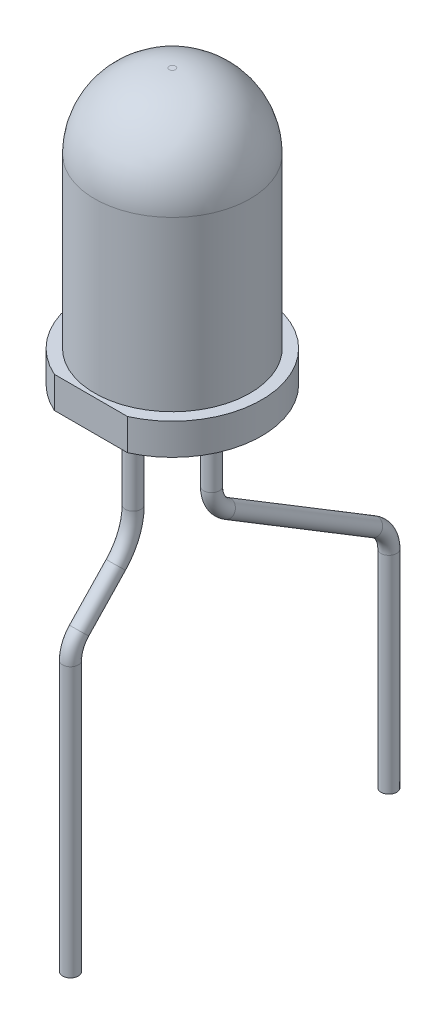
SolidWorks part; units mm, degrees
material "Perspex (TM) GS Acrylic Cast Sheet"
ref_plane "Front Plane" through (0, 0, 0) normal (0, 0, 1) x (1, 0, 0)
ref_plane "Top Plane" through (0, 0, 0) normal (0, 1, 0) x (1, 0, 0)
ref_plane "Right Plane" through (0, 0, 0) normal (1, 0, 0) x (0, 0, -1)
sketch "Sketch1" plane through (0, 0, 0) normal (0, 0, 1) x (1, 0, 0)
  line L0 (0, 0) -> (0, 8.75)
  line L1 (0, 0) -> (2.85, 0)
  line L2 (2.85, 0) -> (2.85, 1)
  line L3 (2.85, 1) -> (2.48, 1)
  line L4 (2.48, 1) -> (2.48, 6.37)
  line L5 (0, 8.75) -> (0.1, 8.75)
  arc A0 (2.48, 6.37) -> (0.1, 8.75) centre (0.1, 6.37) ccw
  dimension "D5" = 0.1
  dimension "D1" = 8.75
  dimension "D2" = 2.85
  dimension "D3" = 2.48
  dimension "D4" = 1
revolve "Revolve1" add sketch "Sketch1" angle 360 about L0
sketch "Sketch2" plane through (0, 0, 0) normal (0, -1, 0) x (1, 0, 0)
  line L0 (0, 0) -> (0, 2.6) construction
  line L1 (-1.1673, 2.6) -> (1.1673, 2.6)
  line L2 (0, 2.6) -> (0, 2.85) construction
  line L3 (0, 0) -> (0, -2.85) construction
  circle A0 centre (0, 0) radius 2.85 construction
  arc A1 (1.1673, 2.6) -> (-1.1673, 2.6) centre (0, 0) ccw
  dimension "D1" = 5.45
extrude "Cut-Extrude1" cut sketch "Sketch2" against normal up to surface (1 mm away) up to face at (0, 1, -2.48)
sketch "Sketch3" plane through (0, 0, 0) normal (0, -1, 0) x (1, 0, 0)
  line L0 (0, 1.25) -> (0, -1.25) construction
  circle A0 centre (0, -1.25) radius 0.25
  circle A1 centre (0, 1.25) radius 0.25
  dimension "D2" = 0.5
  dimension "D1" = 2.5
extrude "Boss-Extrude1" add sketch "Sketch3" along normal blind 2
sketch "Sketch4" plane through (0, 0, 0) normal (1, 0, 0) x (0, 0, -1)
  line L0 (-1.25, -2) -> (-1.25, 0) construction
  line L1 (-1.5, -2) -> (-1, -2) construction
  line L2 (-1.5, 0) -> (-1, 0) construction
  line L3 (1.25, -2) -> (1.25, 0) construction
  line L4 (1, -2) -> (1.5, -2) construction
  line L5 (1, 0) -> (1.5, 0) construction
  line L6 (-1.25, -2) -> (-1.25, -2.7)
  line L7 (-1.8017, -4.0793) -> (-2.9741, -5.3103)
  line L8 (-3.25, -6) -> (-3.25, -14.6)
  line L9 (1.25, -2) -> (1.25, -3.4373) construction
  line L10 (1.7309, -4.2921) -> (6.4291, -7.1453) construction
  line L11 (6.91, -8) -> (6.91, -14.6) construction
  line L12 (-3.25, -14.6) -> (6.91, -14.6) construction
  arc A0 (-1.25, -2.7) -> (-1.8017, -4.0793) centre (-3.25, -2.7) cw
  arc A1 (-2.9741, -5.3103) -> (-3.25, -6) centre (-2.25, -6) ccw
  arc A2 (1.25, -3.4373) -> (1.7309, -4.2921) centre (2.25, -3.4373) ccw construction
  arc A3 (6.4291, -7.1453) -> (6.91, -8) centre (5.91, -8) cw construction
  point P22 (-1.25, -3.5)
  point P25 (-3.25, -5.6)
  point P28 (1.25, -4)
  point P31 (6.91, -7.4373)
  dimension "D8" = 2
  dimension "D9" = 1
  dimension "D10" = 1
  dimension "D11" = 1
  dimension "D1" = 1.5
  dimension "D2" = 2
  dimension "D3" = 9
  dimension "D5" = 2
  dimension "D6" = 10.16
  dimension "D7" = 6
  dimension "D12" = 8
ref_plane "Plane1" through (0, -14.6, 3.25) normal (0, -1, 0) x (-1, 0, 0)
sketch "Sketch5" plane through (0, -14.6, 3.25) normal (0, -1, 0) x (-1, 0, 0)
  circle A0 centre (0, 0) radius 0.25
  dimension "D1" = 0.5
sweep "Sweep1" add profiles "Sketch5" path "Sketch4"
sketch "Sketch6" plane through (0, 0, 0) normal (1, 0, 0) x (0, 0, -1)
  line L0 (6.91, -8) -> (6.91, -14.6) construction
  line L1 (1.7309, -4.2921) -> (6.4291, -7.1453) construction
  line L2 (1.25, -2) -> (1.25, -3.4373) construction
  line L3 (6.91, -8) -> (6.91, -14.6)
  line L4 (1.7309, -4.2921) -> (6.4291, -7.1453)
  line L5 (1.25, -2) -> (1.25, -3.4373)
  arc A0 (6.91, -8) -> (6.4291, -7.1453) centre (5.91, -8) ccw construction
  arc A1 (1.25, -3.4373) -> (1.7309, -4.2921) centre (2.25, -3.4373) ccw construction
  arc A2 (6.91, -8) -> (6.4291, -7.1453) centre (5.91, -8) ccw
  arc A3 (1.25, -3.4373) -> (1.7309, -4.2921) centre (2.25, -3.4373) ccw
ref_plane "Plane2" through (0, -14.6, -6.91) normal (0, -1, 0) x (-1, 0, 0)
sketch "Sketch7" plane through (0, -14.6, -6.91) normal (0, -1, 0) x (-1, 0, 0)
  circle A0 centre (0, 0) radius 0.25
  dimension "D1" = 0.5
sweep "Sweep2" add profiles "Sketch7" path "Sketch6"
sketch "Sketch8" plane through (0, 0, 0) normal (0, -1, 0) x (1, 0, 0)
  circle A0 centre (0, 1.25) radius 0.25 construction
  circle A1 centre (0, 1.25) radius 0.25
  circle A2 centre (0, -1.25) radius 0.25 construction
  circle A3 centre (0, -1.25) radius 0.25
extrude "Boss-Extrude2" add sketch "Sketch8" against normal blind 3 separate body
sketch "Sketch11" plane through (0, 3, 0) normal (0, 1, 0) x (1, 0, 0)
  circle A1 centre (0, 1.25) radius 0.25
  circle A2 centre (0, 1.25) radius 0.25
  dimension "D1" = 0
extrude "Cut-Extrude2" cut sketch "Sketch11" against normal blind 1.5
sketch "Sketch9" plane through (0, 3, 0) normal (0, 1, 0) x (1, 0, 0)
  circle A0 centre (0, -1.25) radius 0.5
  dimension "D1" = 1
extrude "Boss-Extrude3" add sketch "Sketch9" along normal blind 0.2
fillet "Fillet1" radius 0.15 1 edges at (0, 3.2, 1.75)
sketch "Sketch10" plane through (0, 0, 0) normal (1, 0, 0) x (0, 0, -1)
  line L0 (-1.25, 3) -> (-1.25, 1.4)
  line L1 (-1.5, 3) -> (-1, 3) construction
  line L2 (-1.25, 1.4) -> (-0.75, 1.4)
  line L3 (0.3972, 1.7617) -> (1.4079, 2.4694)
  line L4 (1.3898, 2.6433) -> (0.9317, 2.8391)
  line L5 (0.1457, 3) -> (-1.25, 3)
  line L6 (1.45, 2.5617) -> (-1.25, 2.5617) construction
  line L7 (1.5, 1.5) -> (1.5, 2.1)
  line L8 (1.5, 1.5) -> (1.5, 1.1)
  line L9 (1.5, 0) -> (1.5, 1.5) construction
  line L10 (1.5, 1.1) -> (0.9, 1.1)
  line L11 (0.9, 1.1) -> (0.9, 1.7)
  line L12 (0.9, 1.7) -> (1.5, 2.1) construction
  line L13 (1.5, 1.5) -> (1, 1.5) construction
  arc A0 (1.4079, 2.4694) -> (1.3898, 2.6433) centre (1.3505, 2.5513) ccw
  arc A1 (0.9317, 2.8391) -> (0.1457, 3) centre (0.1457, 1) ccw
  arc A2 (-0.75, 1.4) -> (0.3972, 1.7617) centre (-0.75, 3.4) ccw
  arc A3 (1.5, 2.1) -> (0.9, 1.7) centre (0.934, 2.299) cw
  dimension "D2" = 0.1
  dimension "D3" = 2
  dimension "D4" = 2.7
  dimension "D12" = 0.6
  dimension "D1" = 1.6
  dimension "D5" = 35
  dimension "D6" = 1.3957
  dimension "D7" = 0.5
  dimension "D8" = 1
  dimension "D9" = 0.4
  dimension "D10" = 0.6
  dimension "D11" = 0.6
extrude "Boss-Extrude4" add sketch "Sketch10" along normal mid plane 0.3
fillet "Fillet2" radius 0.1 4 edges at (0, 1.1, -1.5) (0, 1.1, -0.9) (0, 1.7, -0.9) (0, 2.1, -1.5)
fillet "Fillet3" radius 0.1 1 edges at (0, 1.5, -1)
